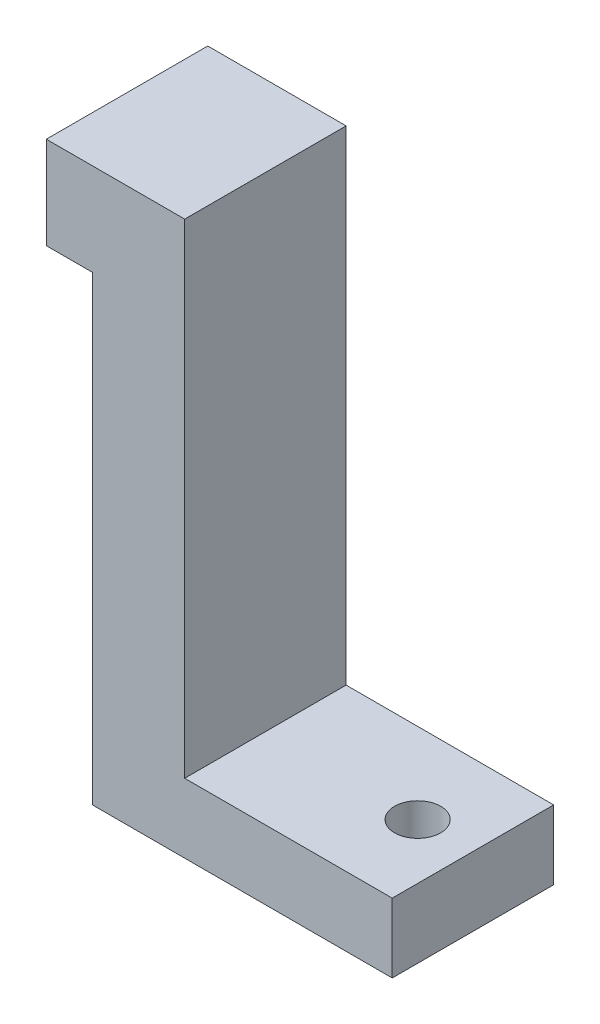
SolidWorks part; units mm, degrees
ref_plane "Front Plane" through (0, 0, 0) normal (0, 0, 1) x (1, 0, 0)
ref_plane "Top Plane" through (0, 0, 0) normal (0, 1, 0) x (1, 0, 0)
ref_plane "Right Plane" through (0, 0, 0) normal (1, 0, 0) x (0, 0, -1)
sketch "Sketch1" plane through (0, 0, 0) normal (0, 0, 1) x (1, 0, 0)
  line L0 (-0.5, 3) -> (-0.5, 2)
  line L1 (-0.5, 3) -> (0.5, 3)
  line L2 (-0.5, 3) -> (-0.5, -3)
  line L3 (-0.5, -3) -> (0.5, -3)
  line L4 (0.5, 3) -> (0.5, -3)
  line L5 (-0.5, 3) -> (0.5, -3) construction
  line L6 (-0.5, -3) -> (0.5, 3) construction
  line L7 (-0.5, 3) -> (-1, 3)
  line L8 (-0.5, 2) -> (-1, 2)
  line L9 (-1, 3) -> (-1, 2)
  line L10 (0.5, -3) -> (0.5, -2.25)
  line L11 (0.5, -3) -> (2.75, -3)
  line L12 (0.5, -2.25) -> (2.75, -2.25)
  line L13 (2.75, -3) -> (2.75, -2.25)
  point P0 (0, 0)
  dimension "D1" = 1
  dimension "D2" = 6
  dimension "D3" = 0.75
  dimension "D4" = 2.25
  dimension "D5" = 1
  dimension "D6" = 0.5
extrude "Boss-Extrude1" add sketch "Sketch1" along normal blind 0.75 and the other way blind 1 contours L4 L1 L0 L2 L3 | L7 L9 L8 L0 | L11 L13 L12 L4
ref_plane "mid_plane" through (0, 0, -0.125) normal (0, 0, -1) x (-1, 0, 0)
hole_wizard "Ø0.5 (0.5) Diameter Hole1" positions "Sketch4" profile "Sketch5" hole size "Ø0.5" standard "ANSI Metric" end condition up to next
sketch "Sketch4" plane through (0, -2.25, 0) normal (0, 1, 0) x (1, 0, 0)
  line L0 (2.0625, 0.125) -> (-2.0625, 0.125) construction
  line L1 (2.75, 1) -> (2.75, -0.75) construction
  point P0 (2.15, 0.125)
  point P7 (2.75, 0.125)
  dimension "D1" = 0
  dimension "D2" = 0.6
sketch "Sketch5" plane through (2.15, -2.25, -0.125) normal (1, 0, 0) x (0, 0, 1)
  line L0 (0, 0) -> (0, 0.75)
  line L1 (0, 0.75) -> (0.25, 0.75)
  line L2 (0.25, 0.75) -> (0.25, 0)
  line L5 (0.25, 0) -> (0, 0)
  line L11 (0, -6.35) -> (0, 107.95) construction
  dimension "Thru Hole Dia." = 0.5
  dimension "Thru Hole Depth" = 0.75
